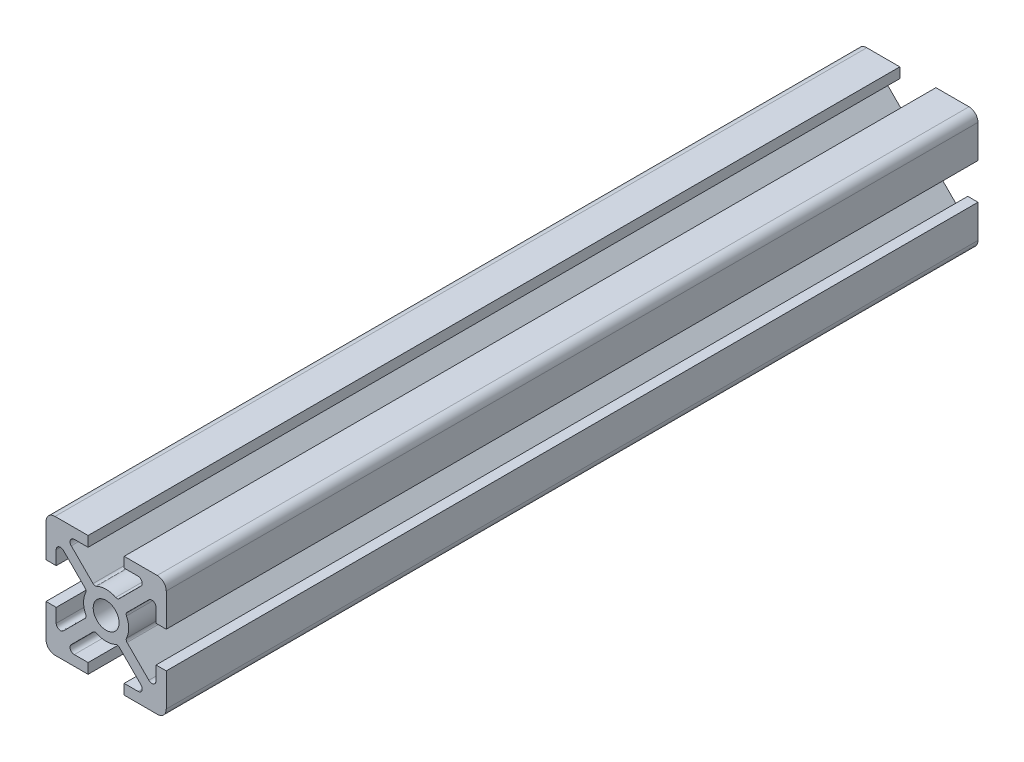
SolidWorks part; units mm, degrees
material "6063-T5"
ref_plane "Face" through (0, 0, 0) normal (0, 0, 1) x (1, 0, 0)
ref_plane "Dessus" through (0, 0, 0) normal (0, 1, 0) x (1, 0, 0)
ref_plane "Droite" through (0, 0, 0) normal (1, 0, 0) x (0, 0, -1)
sketch "Esquisse1" plane through (0, 0, 0) normal (0, 0, 1) x (1, 0, 0)
  line L0 (-3, 10) -> (-8.5, 10)
  line L2 (-3, -10) -> (-3, -8.3)
  line L3 (-3, -8.3) -> (-5.2994, -8.3)
  line L4 (-5.7944, -7.105) -> (-2.1755, -3.4861)
  line L6 (2.1755, -3.4861) -> (5.7944, -7.105)
  line L7 (5.2994, -8.3) -> (3, -8.3)
  line L8 (3, -8.3) -> (3, -10)
  line L11 (3, -10) -> (8.5, -10)
  line L12 (10, -8.5) -> (10, -3)
  line L15 (10, -3) -> (8.3, -3)
  line L16 (8.3, -3) -> (8.3, -5.2994)
  line L17 (7.105, -5.7944) -> (3.4861, -2.1755)
  line L20 (3.4861, 2.1755) -> (7.105, 5.7944)
  line L21 (8.3, 5.2994) -> (8.3, 3)
  line L22 (8.3, 3) -> (10, 3)
  line L25 (10, 3) -> (10, 8.5)
  line L26 (8.5, 10) -> (3.5, 10)
  line L29 (3, 10) -> (3, 8.3)
  line L30 (3, 8.3) -> (5.2994, 8.3)
  line L31 (5.7944, 7.105) -> (2.1755, 3.4861)
  line L34 (-2.1755, 3.4861) -> (-5.7944, 7.105)
  line L35 (-5.2994, 8.3) -> (-3, 8.3)
  line L36 (-3, 8.3) -> (-3, 10)
  line L39 (3.5, 10) -> (3, 10)
  line L40 (-10, 8.5) -> (-10, 3)
  line L43 (-10, 3) -> (-8.3, 3)
  line L44 (-8.3, 3) -> (-8.3, 5.2994)
  line L45 (-7.105, 5.7944) -> (-3.4861, 2.1755)
  line L48 (-3.4861, -2.1755) -> (-7.105, -5.7944)
  line L49 (-8.3, -5.2994) -> (-8.3, -3)
  line L50 (-8.3, -3) -> (-10, -3)
  line L53 (-10, -3) -> (-10, -8.5)
  line L54 (-8.5, -10) -> (-3, -10)
  line L55 (13.1941, 0) -> (-16.3684, 0) construction
  line L56 (0, 3.75) -> (0, -15.1011) construction
  line L58 (5.7944, 5.7944) -> (-5.2994, -5.2994) construction
  line L59 (5.7944, -5.7944) -> (-5.4107, 5.4107) construction
  circle A0 centre (0, 0) radius 2.15
  arc A1 (-5.2994, -8.3) -> (-5.7944, -7.105) centre (-5.2994, -7.6) cw
  arc A2 (-2.1755, -3.4861) -> (-1.6076, -3.388) centre (-1.8219, -3.8397) cw
  arc A3 (-1.6076, -3.388) -> (1.6076, -3.388) centre (0, 0) ccw
  arc A5 (1.6076, -3.388) -> (2.1755, -3.4861) centre (1.8219, -3.8397) cw
  arc A6 (5.7944, -7.105) -> (5.2994, -8.3) centre (5.2994, -7.6) cw
  arc A7 (8.5, -10) -> (10, -8.5) centre (8.5, -8.5) ccw
  arc A8 (8.3, -5.2994) -> (7.105, -5.7944) centre (7.6, -5.2994) cw
  arc A9 (3.4861, -2.1755) -> (3.388, -1.6076) centre (3.8397, -1.8219) cw
  arc A10 (3.388, -1.6076) -> (3.75, 0) centre (0, 0) ccw
  arc A11 (3.75, 0) -> (3.388, 1.6076) centre (0, 0) ccw
  arc A12 (3.388, 1.6076) -> (3.4861, 2.1755) centre (3.8397, 1.8219) cw
  arc A13 (7.105, 5.7944) -> (8.3, 5.2994) centre (7.6, 5.2994) cw
  arc A14 (10, 8.5) -> (8.5, 10) centre (8.5, 8.5) ccw
  arc A15 (5.2994, 8.3) -> (5.7944, 7.105) centre (5.2994, 7.6) cw
  arc A16 (2.1755, 3.4861) -> (1.6076, 3.388) centre (1.8219, 3.8397) cw
  arc A17 (1.6076, 3.388) -> (-1.6076, 3.388) centre (0, 0) ccw
  arc A19 (-1.6076, 3.388) -> (-2.1755, 3.4861) centre (-1.8219, 3.8397) cw
  arc A20 (-5.7944, 7.105) -> (-5.2994, 8.3) centre (-5.2994, 7.6) cw
  arc A21 (-8.5, 10) -> (-10, 8.5) centre (-8.5, 8.5) ccw
  arc A22 (-8.3, 5.2994) -> (-7.105, 5.7944) centre (-7.6, 5.2994) cw
  arc A23 (-3.4861, 2.1755) -> (-3.388, 1.6076) centre (-3.8397, 1.8219) cw
  arc A24 (-3.388, 1.6076) -> (-3.388, -1.6076) centre (0, 0) ccw
  arc A26 (-3.388, -1.6076) -> (-3.4861, -2.1755) centre (-3.8397, -1.8219) cw
  arc A27 (-7.105, -5.7944) -> (-8.3, -5.2994) centre (-7.6, -5.2994) cw
  arc A28 (-10, -8.5) -> (-8.5, -10) centre (-8.5, -8.5) ccw
  dimension "D3" = 4.3
  dimension "D4" = 1.5
  dimension "D15" = 0.7
  dimension "D19" = 3.75
  dimension "D20" = 0.5
  dimension "D1" = 20
  dimension "D2" = 20
  dimension "D10" = 10
  dimension "D11" = 10
  dimension "D12" = 3
  dimension "D13" = 3
  dimension "D16" = 1.7
  dimension "D17" = 5.2994
  dimension "D18" = 45
  dimension "D22" = 45
  dimension "D23" = 6
  dimension "D24" = 45
  dimension "D25" = 5.2994
  dimension "D26" = 45
extrude "Boss.-Extru.1" add sketch "Esquisse1" along normal blind 135
